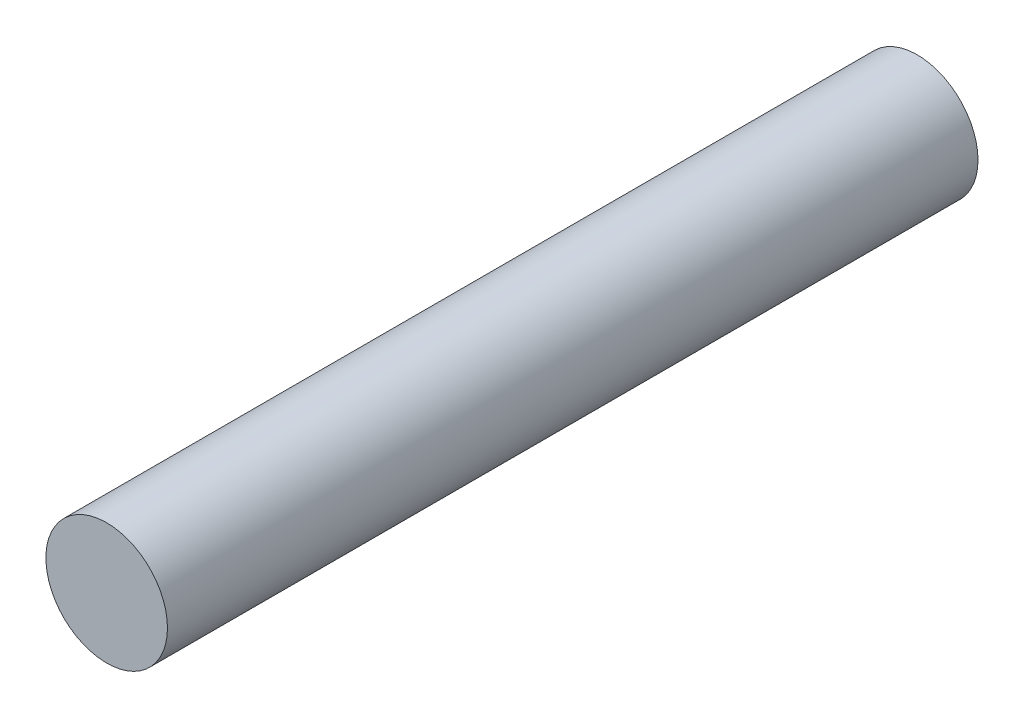
SolidWorks part; units mm, degrees
ref_plane "Front" through (0, 0, 0) normal (0, 0, 1) x (1, 0, 0)
ref_plane "Top" through (0, 0, 0) normal (0, 1, 0) x (1, 0, 0)
ref_plane "Right" through (0, 0, 0) normal (1, 0, 0) x (0, 0, -1)
sketch "草图1" plane through (0, 0, 0) normal (0, 0, 1) x (1, 0, 0)
  circle A0 centre (0, 0) radius 1.5
  dimension "D1" = 3
extrude "凸台-拉伸1" add sketch "草图1" along normal blind 20
